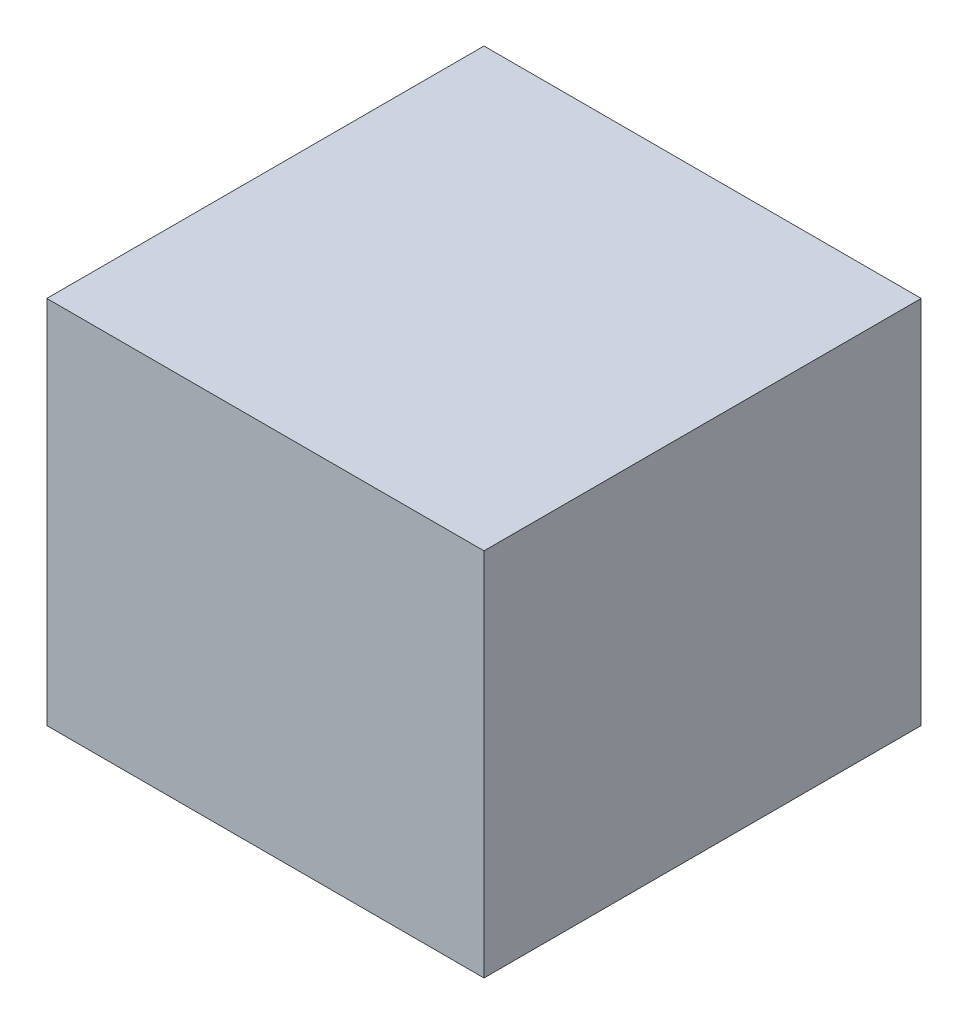
SolidWorks part; units mm, degrees
ref_plane "Front Plane" through (0, 0, 0) normal (0, 0, 1) x (1, 0, 0)
ref_plane "Top Plane" through (0, 0, 0) normal (0, 1, 0) x (1, 0, 0)
ref_plane "Right Plane" through (0, 0, 0) normal (1, 0, 0) x (0, 0, -1)
sketch "Sketch1" plane through (0, 0, 0) normal (0, 1, 0) x (1, 0, 0)
  line L1 (0, 0) -> (-330.2, 0)
  line L2 (0, 0) -> (0, 330.2)
  line L3 (0, 330.2) -> (-330.2, 330.2)
  line L4 (-330.2, 0) -> (-330.2, 330.2)
  dimension "D1" = 330.2
  dimension "D2" = 330.2
extrude "Boss-Extrude1" add sketch "Sketch1" along normal blind 279.4
